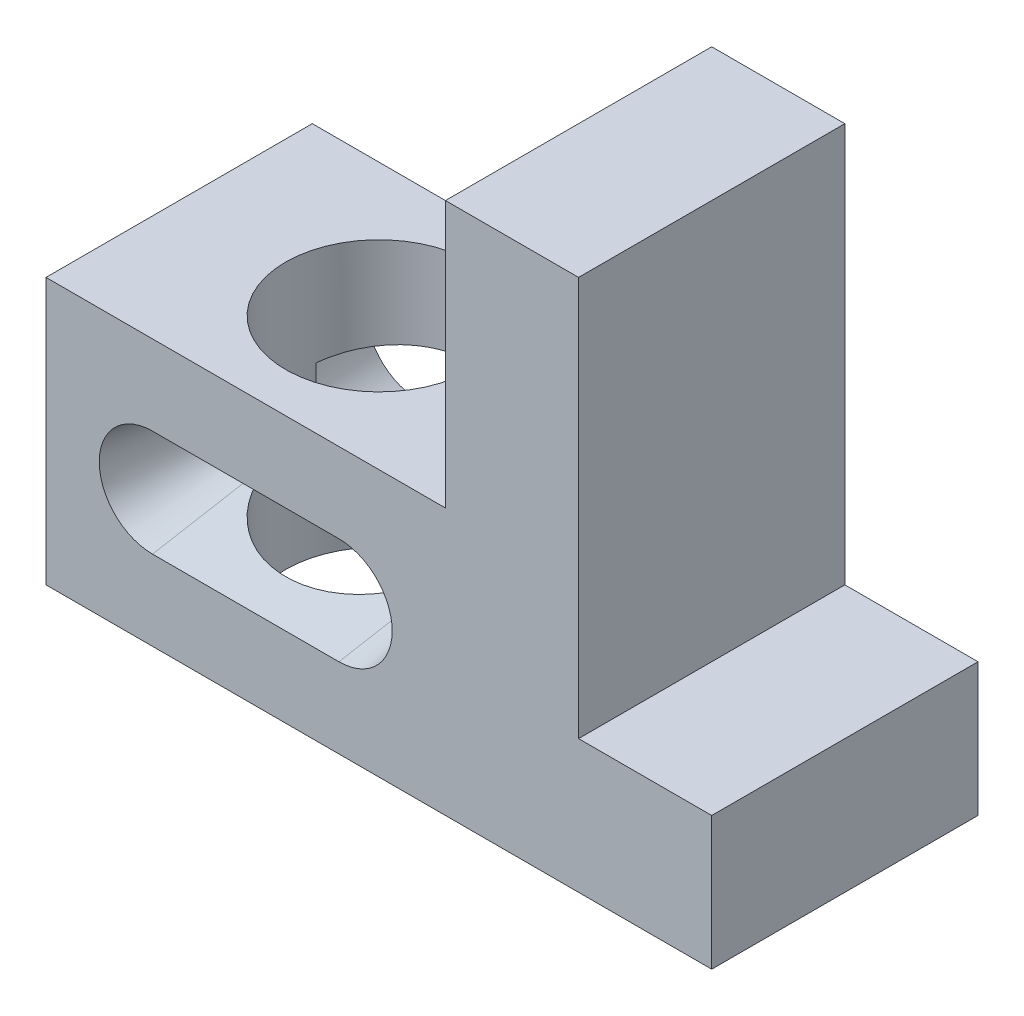
SolidWorks part; units mm, degrees
ref_plane "Front Plane" through (0, 0, 0) normal (0, 0, 1) x (1, 0, 0)
ref_plane "Top Plane" through (0, 0, 0) normal (0, 1, 0) x (1, 0, 0)
ref_plane "Right Plane" through (0, 0, 0) normal (1, 0, 0) x (0, 0, -1)
sketch "Sketch1" plane through (0, 0, 0) normal (0, 0, 1) x (1, 0, 0)
  line L0 (-50.7317, 0) -> (74.2683, 0)
  line L1 (74.2683, 0) -> (74.2683, 25)
  line L2 (74.2683, 25) -> (49.2683, 25)
  line L3 (49.2683, 25) -> (49.2683, 100)
  line L4 (49.2683, 100) -> (24.2683, 100)
  line L5 (24.2683, 100) -> (24.2683, 50)
  line L6 (24.2683, 50) -> (-50.7317, 50)
  line L7 (-50.7317, 50) -> (-50.7317, 0)
  dimension "D1" = 50
  dimension "D2" = 75
  dimension "D3" = 100
  dimension "D4" = 25
extrude "Boss-Extrude1" add sketch "Sketch1" along normal blind 50
sketch "Sketch2" plane through (0, 0, 50) normal (0, 0, 1) x (1, 0, 0)
  line L0 (-30.7317, 35) -> (4.2683, 35)
  line L1 (-30.7317, 15) -> (4.2683, 15)
  line L2 (-30.7317, 25) -> (4.2683, 25) construction
  line L4 (-50.7317, 50) -> (-50.7317, 0) construction
  line L6 (-50.7317, 50) -> (-50.7317, 0) construction
  line L7 (-50.7317, 0) -> (74.2683, 0) construction
  arc A0 (4.2683, 15) -> (4.2683, 35) centre (4.2683, 25) ccw
  arc A1 (-30.7317, 35) -> (-30.7317, 15) centre (-30.7317, 25) ccw
  point P13 (-13.2317, 25)
  dimension "D2" = 10
  dimension "D1" = 35
  dimension "D3" = 25
  dimension "D4" = 37.5
extrude "Cut-Extrude1" cut sketch "Sketch2" against normal blind 20 draft 10
sketch "Sketch3" plane through (0, 0, 0) normal (0, 0, -1) x (-1, 0, 0)
  line L0 (-4.2683, 35) -> (30.7317, 35) construction
  line L1 (30.7317, 15) -> (-4.2683, 15) construction
  line L2 (-4.2683, 35) -> (30.7317, 35)
  line L3 (30.7317, 15) -> (-4.2683, 15)
  arc A0 (-4.2683, 35) -> (-4.2683, 15) centre (-4.2683, 25) ccw construction
  arc A1 (30.7317, 15) -> (30.7317, 35) centre (30.7317, 25) ccw construction
  arc A2 (-4.2683, 35) -> (-4.2683, 15) centre (-4.2683, 25) ccw
  arc A3 (30.7317, 15) -> (30.7317, 35) centre (30.7317, 25) ccw
extrude "Cut-Extrude2" cut sketch "Sketch3" against normal blind 20 draft 10
sketch "Sketch4" plane through (0, 50, 0) normal (0, 1, 0) x (1, 0, 0)
  line L0 (24.2683, 0) -> (-50.7317, 0) construction
  line L1 (-50.7317, -50) -> (-50.7317, 0) construction
  circle A0 centre (-13.2317, -25) radius 17.5
  dimension "D1" = 35
  dimension "D2" = 25
  dimension "D3" = 37.5
extrude "Cut-Extrude3" cut sketch "Sketch4" against normal blind 60
